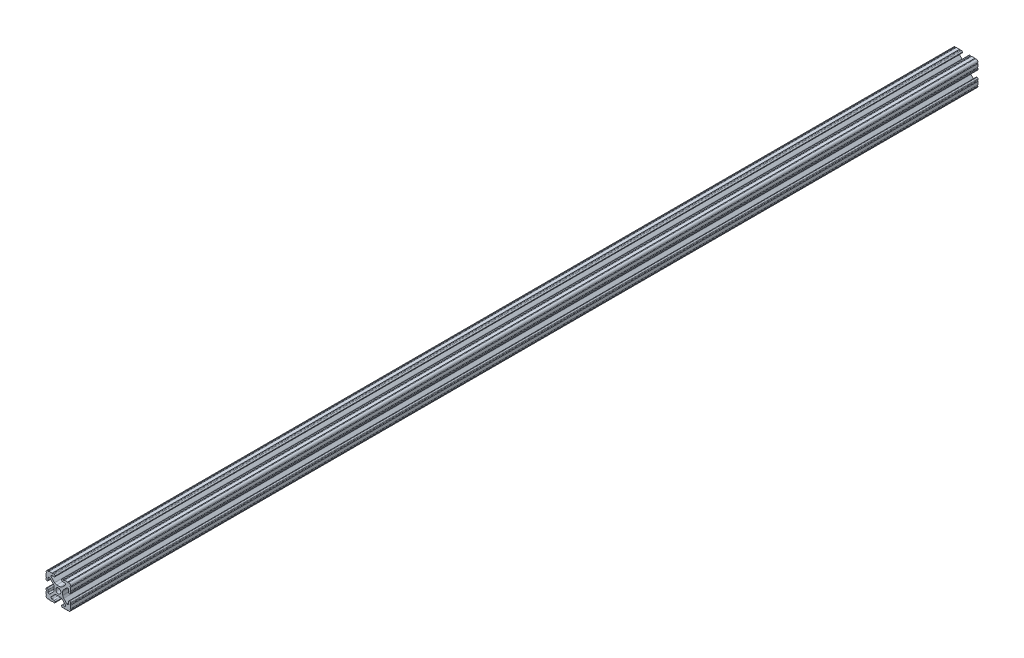
SolidWorks part; units mm, degrees
ref_plane "Front Plane" through (0, 0, 0) normal (0, 0, 1) x (1, 0, 0)
ref_plane "Top Plane" through (0, 0, 0) normal (0, 1, 0) x (1, 0, 0)
ref_plane "Right Plane" through (0, 0, 0) normal (1, 0, 0) x (0, 0, -1)
sketch "Sketch1" plane through (0, 0, 0) normal (0, 0, 1) x (1, 0, 0)
  line L88 (-7.1797, -8.6452) -> (-3.9523, -5.4237)
  line L89 (-1.7093, -4.4958) -> (1.7093, -4.4958)
  line L90 (3.9523, -5.4237) -> (7.1797, -8.6452)
  line L91 (6.4164, -10.4902) -> (4.2875, -10.4902)
  line L92 (3.2385, -11.5392) -> (3.2385, -11.651)
  line L93 (4.2875, -12.7) -> (5.3171, -12.7)
  line L94 (6.3331, -12.7) -> (9.5504, -12.7)
  line L95 (12.7, -9.5504) -> (12.7, -6.3331)
  line L96 (12.7, -5.3171) -> (12.7, -4.2875)
  line L97 (11.651, -3.2385) -> (11.5392, -3.2385)
  line L98 (10.4902, -4.2875) -> (10.4902, -6.4021)
  line L99 (8.7371, -7.1294) -> (5.441, -3.8408)
  line L100 (4.5085, -1.5932) -> (4.5085, 1.5932)
  line L101 (5.441, 3.8408) -> (8.7371, 7.1294)
  line L102 (10.4902, 6.4021) -> (10.4902, 4.2875)
  line L103 (11.5392, 3.2385) -> (11.651, 3.2385)
  line L104 (12.7, 4.2875) -> (12.7, 5.3171)
  line L105 (12.7, 6.3331) -> (12.7, 9.5504)
  line L106 (9.5504, 12.7) -> (6.3331, 12.7)
  line L107 (5.3171, 12.7) -> (4.2875, 12.7)
  line L108 (3.2385, 11.651) -> (3.2385, 11.5392)
  line L109 (4.2875, 10.4902) -> (6.4768, 10.4902)
  line L110 (7.207, 8.7244) -> (3.8983, 5.4232)
  line L111 (1.6558, 4.4958) -> (-1.6558, 4.4958)
  line L112 (-3.8983, 5.4232) -> (-7.207, 8.7244)
  line L113 (-6.4768, 10.4902) -> (-4.2875, 10.4902)
  line L114 (-3.2385, 11.5392) -> (-3.2385, 11.651)
  line L115 (-4.2875, 12.7) -> (-5.3171, 12.7)
  line L116 (-6.3331, 12.7) -> (-9.5504, 12.7)
  line L117 (-12.7, 9.5504) -> (-12.7, 6.3331)
  line L118 (-12.7, 5.3171) -> (-12.7, 4.2875)
  line L119 (-11.651, 3.2385) -> (-11.5392, 3.2385)
  line L120 (-10.4902, 4.2875) -> (-10.4902, 6.4021)
  line L121 (-8.7371, 7.1294) -> (-5.441, 3.8408)
  line L122 (-4.5085, 1.5932) -> (-4.5085, -1.5932)
  line L123 (-5.441, -3.8408) -> (-8.7371, -7.1294)
  line L124 (-10.4902, -6.4021) -> (-10.4902, -4.2875)
  line L125 (-11.5392, -3.2385) -> (-11.651, -3.2385)
  line L126 (-12.7, -4.2875) -> (-12.7, -5.3171)
  line L127 (-12.7, -6.3331) -> (-12.7, -9.5504)
  line L128 (-9.5504, -12.7) -> (-6.3331, -12.7)
  line L129 (-5.3171, -12.7) -> (-4.2875, -12.7)
  line L130 (-3.2385, -11.651) -> (-3.2385, -11.5392)
  line L131 (-4.2875, -10.4902) -> (-6.4164, -10.4902)
  circle A1 centre (0, 0) radius 2.6035
  arc A104 (-7.1797, -8.6452) -> (-6.4164, -10.4902) centre (-6.4164, -9.4098) ccw
  arc A105 (-1.7093, -4.4958) -> (-3.9523, -5.4237) centre (-1.7093, -7.6708) ccw
  arc A106 (3.9523, -5.4237) -> (1.7093, -4.4958) centre (1.7093, -7.6708) ccw
  arc A107 (6.4164, -10.4902) -> (7.1797, -8.6452) centre (6.4164, -9.4098) ccw
  arc A108 (4.2875, -10.4902) -> (3.2385, -11.5392) centre (4.2875, -11.5392) ccw
  arc A109 (3.2385, -11.651) -> (4.2875, -12.7) centre (4.2875, -11.651) ccw
  arc A110 (6.3331, -12.7) -> (5.3171, -12.7) centre (5.8251, -12.7) ccw
  arc A111 (10.5664, -12.6998) -> (9.5504, -12.7) centre (10.0584, -12.7) ccw
  arc A112 (10.5664, -12.6998) -> (12.6998, -10.5664) centre (10.5918, -10.5918) ccw
  arc A113 (12.7, -9.5504) -> (12.6998, -10.5664) centre (12.7, -10.0584) ccw
  arc A114 (12.7, -5.3171) -> (12.7, -6.3331) centre (12.7, -5.8251) ccw
  arc A115 (12.7, -4.2875) -> (11.651, -3.2385) centre (11.651, -4.2875) ccw
  arc A116 (11.5392, -3.2385) -> (10.4902, -4.2875) centre (11.5392, -4.2875) ccw
  arc A117 (8.7371, -7.1294) -> (10.4902, -6.4021) centre (9.4628, -6.4021) ccw
  arc A118 (4.5085, -1.5932) -> (5.441, -3.8408) centre (7.6835, -1.5932) ccw
  arc A119 (5.441, 3.8408) -> (4.5085, 1.5932) centre (7.6835, 1.5932) ccw
  arc A120 (10.4902, 6.4021) -> (8.7371, 7.1294) centre (9.4628, 6.4021) ccw
  arc A121 (10.4902, 4.2875) -> (11.5392, 3.2385) centre (11.5392, 4.2875) ccw
  arc A122 (11.651, 3.2385) -> (12.7, 4.2875) centre (11.651, 4.2875) ccw
  arc A123 (12.7, 6.3331) -> (12.7, 5.3171) centre (12.7, 5.8251) ccw
  arc A124 (12.6998, 10.5664) -> (12.7, 9.5504) centre (12.7, 10.0584) ccw
  arc A125 (12.6998, 10.5664) -> (10.5664, 12.6998) centre (10.5918, 10.5918) ccw
  arc A126 (9.5504, 12.7) -> (10.5664, 12.6998) centre (10.0584, 12.7) ccw
  arc A127 (5.3171, 12.7) -> (6.3331, 12.7) centre (5.8251, 12.7) ccw
  arc A128 (4.2875, 12.7) -> (3.2385, 11.651) centre (4.2875, 11.651) ccw
  arc A129 (3.2385, 11.5392) -> (4.2875, 10.4902) centre (4.2875, 11.5392) ccw
  arc A130 (7.207, 8.7244) -> (6.4768, 10.4902) centre (6.4768, 9.4563) ccw
  arc A131 (1.6558, 4.4958) -> (3.8983, 5.4232) centre (1.6558, 7.6708) ccw
  arc A132 (-3.8983, 5.4232) -> (-1.6558, 4.4958) centre (-1.6558, 7.6708) ccw
  arc A133 (-6.4768, 10.4902) -> (-7.207, 8.7244) centre (-6.4768, 9.4563) ccw
  arc A134 (-4.2875, 10.4902) -> (-3.2385, 11.5392) centre (-4.2875, 11.5392) ccw
  arc A135 (-3.2385, 11.651) -> (-4.2875, 12.7) centre (-4.2875, 11.651) ccw
  arc A136 (-6.3331, 12.7) -> (-5.3171, 12.7) centre (-5.8251, 12.7) ccw
  arc A137 (-10.5664, 12.6998) -> (-9.5504, 12.7) centre (-10.0584, 12.7) ccw
  arc A138 (-10.5664, 12.6998) -> (-12.6998, 10.5664) centre (-10.5918, 10.5918) ccw
  arc A139 (-12.7, 9.5504) -> (-12.6998, 10.5664) centre (-12.7, 10.0584) ccw
  arc A140 (-12.7, 5.3171) -> (-12.7, 6.3331) centre (-12.7, 5.8251) ccw
  arc A141 (-12.7, 4.2875) -> (-11.651, 3.2385) centre (-11.651, 4.2875) ccw
  arc A142 (-11.5392, 3.2385) -> (-10.4902, 4.2875) centre (-11.5392, 4.2875) ccw
  arc A143 (-8.7371, 7.1294) -> (-10.4902, 6.4021) centre (-9.4628, 6.4021) ccw
  arc A144 (-4.5085, 1.5932) -> (-5.441, 3.8408) centre (-7.6835, 1.5932) ccw
  arc A145 (-5.441, -3.8408) -> (-4.5085, -1.5932) centre (-7.6835, -1.5932) ccw
  arc A146 (-10.4902, -6.4021) -> (-8.7371, -7.1294) centre (-9.4628, -6.4021) ccw
  arc A147 (-10.4902, -4.2875) -> (-11.5392, -3.2385) centre (-11.5392, -4.2875) ccw
  arc A148 (-11.651, -3.2385) -> (-12.7, -4.2875) centre (-11.651, -4.2875) ccw
  arc A149 (-12.7, -6.3331) -> (-12.7, -5.3171) centre (-12.7, -5.8251) ccw
  arc A150 (-12.6998, -10.5664) -> (-12.7, -9.5504) centre (-12.7, -10.0584) ccw
  arc A151 (-12.6998, -10.5664) -> (-10.5664, -12.6998) centre (-10.5918, -10.5918) ccw
  arc A152 (-9.5504, -12.7) -> (-10.5664, -12.6998) centre (-10.0584, -12.7) ccw
  arc A153 (-5.3171, -12.7) -> (-6.3331, -12.7) centre (-5.8251, -12.7) ccw
  arc A154 (-4.2875, -12.7) -> (-3.2385, -11.651) centre (-4.2875, -11.651) ccw
  arc A155 (-3.2385, -11.5392) -> (-4.2875, -10.4902) centre (-4.2875, -11.5392) ccw
extrude "Boss-Extrude1" add sketch "Sketch1" along normal mid plane 933.45
sketch "Sketch2" plane through (4.5085, 0, 0) normal (1, 0, 0) x (0, 0, -1)
  line L0 (0, 0) -> (-393.7, 0) construction
  line L1 (-466.725, -1.5932) -> (-466.725, 1.5932) construction
  line L2 (0, 0) -> (0, 58.4486) construction
  line L3 (-466.725, 6.3331) -> (-466.725, 9.5504) construction
  circle A0 centre (-282.575, 0) radius 3.175
  circle A1 centre (282.575, 0) radius 3.175
  circle A2 centre (-85.725, 0) radius 3.175
  circle A3 centre (85.725, 0) radius 3.175
  dimension "D1" = 6.35
  dimension "D2" = 184.15
  dimension "D3" = 6.35
  dimension "D4" = 381
extrude "Cut-Extrude1" cut sketch "Sketch2" against normal through all both and the other way through all
